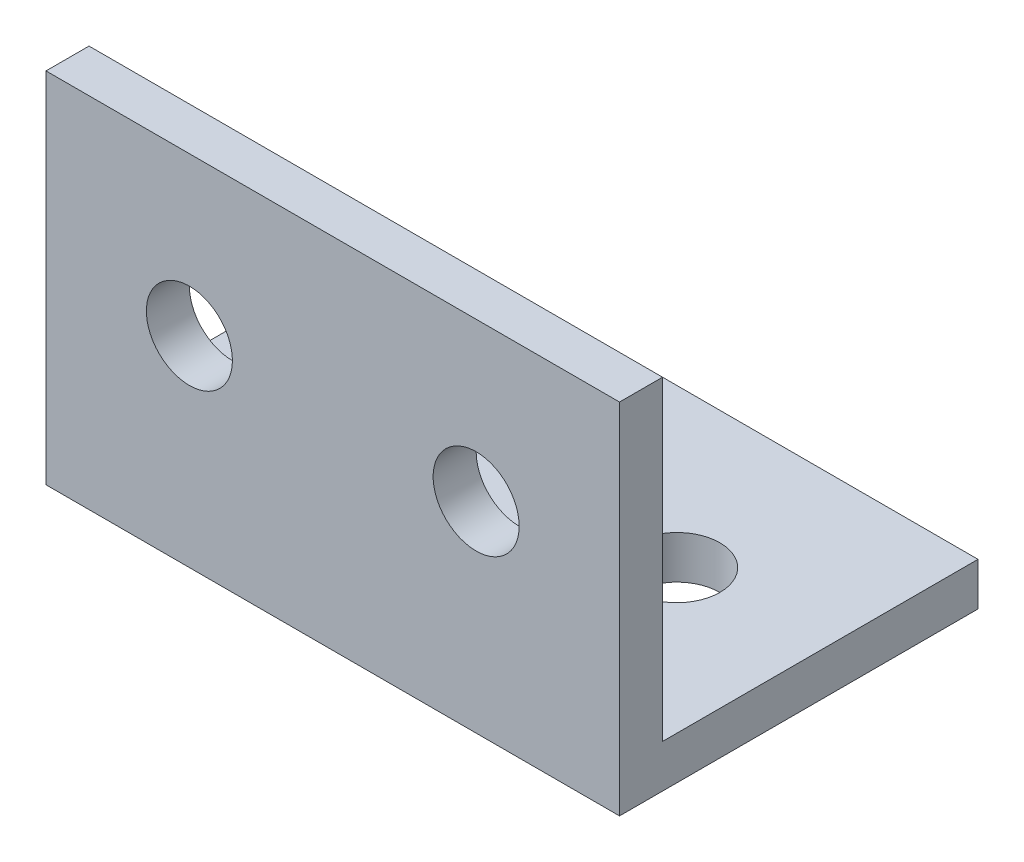
SolidWorks part; units mm, degrees
ref_plane "Спереди" through (0, 0, 0) normal (0, 0, 1) x (1, 0, 0)
ref_plane "Сверху" through (0, 0, 0) normal (0, 1, 0) x (1, 0, 0)
ref_plane "Справа" through (0, 0, 0) normal (1, 0, 0) x (0, 0, -1)
sketch "Эскиз1" plane through (0, 0, 0) normal (1, 0, 0) x (0, 0, -1)
  line L0 (0, 0) -> (0, 25)
  line L1 (0, 0) -> (25, 0)
extrude "Вытянуть-Тонкостенный1" add sketch "Эскиз1" along normal blind 40 thin
sketch "Эскиз2" plane through (0, 0, 0) normal (0, -1, 0) x (1, 0, 0)
  circle A0 centre (10, -14) radius 3
  circle A1 centre (30, -14) radius 3
extrude "Вырез-Вытянуть1" cut sketch "Эскиз2" against normal blind 10
sketch "Эскиз3" plane through (0, 0, 0) normal (0, 0, 1) x (1, 0, 0)
  circle A0 centre (10, 14) radius 3
  circle A1 centre (30, 14) radius 3
extrude "Вырез-Вытянуть2" cut sketch "Эскиз3" against normal blind 10
